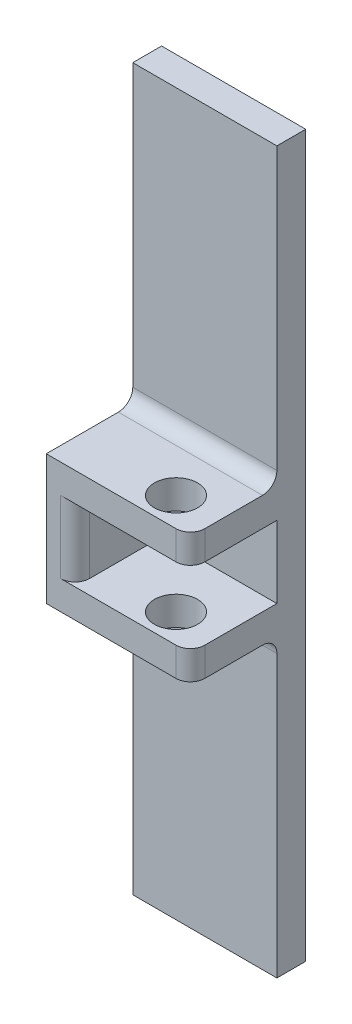
SolidWorks part; units mm, degrees
ref_plane "Front Plane" through (0, 0, 0) normal (0, 0, 1) x (1, 0, 0)
ref_plane "Top Plane" through (0, 0, 0) normal (0, 1, 0) x (1, 0, 0)
ref_plane "Right Plane" through (0, 0, 0) normal (1, 0, 0) x (0, 0, -1)
sketch "Sketch1" plane through (0, 0, 0) normal (0, 0, 1) x (1, 0, 0)
  line L1 (0, 0) -> (10, 0)
  line L2 (0, 0) -> (0, 50)
  line L3 (0, 50) -> (10, 50)
  line L4 (10, 0) -> (10, 50)
  dimension "D1" = 50
  dimension "D2" = 10
extrude "Boss-Extrude1" add sketch "Sketch1" along normal blind 3
chamfer "Chamfer1" distance 1 angle 45 4 edges at (5, 0, 0) (10, 25, 0) (5, 50, 0) (0, 25, 0)
sketch "Sketch2" plane through (0, 0, 3) normal (0, 0, 1) x (1, 0, 0)
  line L0 (10, 0) -> (10, 50) construction
  line L1 (0, 29.5) -> (10, 29.5)
  line L2 (0, 29.5) -> (0, 27.5)
  line L3 (0, 27.5) -> (10, 27.5)
  line L4 (10, 29.5) -> (10, 27.5)
  line L5 (0, 50) -> (0, 0) construction
  line L6 (10, 20.5) -> (10, 22.5)
  line L7 (0, 25) -> (10, 25) construction
  line L8 (0, 22.5) -> (10, 22.5)
  line L9 (0, 20.5) -> (0, 22.5)
  line L10 (0, 20.5) -> (10, 20.5)
  dimension "D1" = 2
  dimension "D2" = 2.5
extrude "Boss-Extrude2" add sketch "Sketch2" along normal blind 6
sketch "Sketch3" plane through (0, 20.5, 0) normal (0, -1, 0) x (1, 0, 0)
  line L0 (0, 3) -> (10, 3) construction
  line L1 (10, 9) -> (10, 3) construction
  circle A0 centre (7, 7) radius 1.5
  dimension "D1" = 3
  dimension "D2" = 4
  dimension "D3" = 3
extrude "Cut-Extrude1" cut sketch "Sketch3" against normal blind 10
fillet "Fillet1" radius 1 2 edges at (10, 28.5, 9) (10, 21.5, 9)
fillet "Fillet2" radius 1 2 edges at (5, 29.5, 3) (5, 20.5, 3)
sketch "Sketch4" plane through (0, 0, 0) normal (-1, 0, 0) x (0, 0, 1)
  line L0 (9, 29.5) -> (9, 27.5) construction
  line L1 (3, 27.5) -> (9, 27.5)
  line L3 (3, 22.5) -> (9, 22.5)
  line L4 (9, 27.5) -> (9, 22.5)
  line L7 (9, 22.5) -> (3, 22.5) construction
  line L8 (3, 27.5) -> (3, 22.5)
extrude "Boss-Extrude3" add sketch "Sketch4" against normal blind 2
fillet "Fillet3" radius 1 1 edges at (2, 25, 9)
